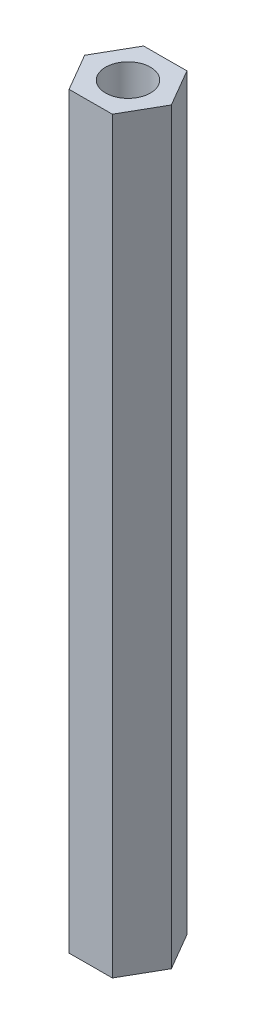
SolidWorks part; units mm, degrees
ref_plane "Ön Düzlem" through (0, 0, 0) normal (0, 0, 1) x (1, 0, 0)
ref_plane "Üst Düzlem" through (0, 0, 0) normal (0, 1, 0) x (1, 0, 0)
ref_plane "Sağ Düzlem" through (0, 0, 0) normal (1, 0, 0) x (0, 0, -1)
sketch "Çizim1" plane through (0, 0, 0) normal (0, 1, 0) x (1, 0, 0)
  line L1 (1.4355, 2.5045) -> (-1.4512, 2.4955)
  line L2 (-1.4512, 2.4955) -> (-2.8867, -0.0091)
  line L3 (-2.8867, -0.0091) -> (-1.4355, -2.5045)
  line L4 (-1.4355, -2.5045) -> (1.4512, -2.4955)
  line L5 (1.4512, -2.4955) -> (2.8867, 0.0091)
  line L6 (2.8867, 0.0091) -> (1.4355, 2.5045)
  circle A0 centre (0, 0) radius 2.5 construction
  dimension "D1" = 5
extrude "Yükseklik-Ekstrüzyon1" add sketch "Çizim1" along normal blind 50
sketch "Çizim2" plane through (0, 50, 0) normal (0, 1, 0) x (1, 0, 0)
  circle A0 centre (0, 0) radius 1.5
  dimension "D1" = 3
extrude "Kes-Ekstrüzyon1" cut sketch "Çizim2" against normal blind 50
